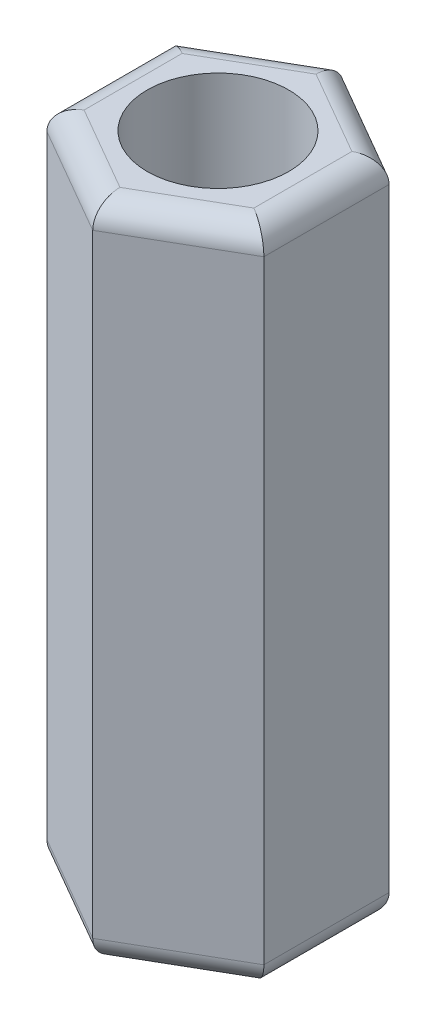
SolidWorks part; units mm, degrees
ref_plane "前视基准面" through (0, 0, 0) normal (0, 0, 1) x (1, 0, 0)
ref_plane "上视基准面" through (0, 0, 0) normal (0, 1, 0) x (1, 0, 0)
ref_plane "右视基准面" through (0, 0, 0) normal (1, 0, 0) x (0, 0, -1)
sketch "草图1" plane through (0, 0, 0) normal (0, 1, 0) x (1, 0, 0)
  line L1 (2.3, -1.3279) -> (2.3, 1.3279)
  line L2 (2.3, 1.3279) -> (0, 2.6558)
  line L3 (0, 2.6558) -> (-2.3, 1.3279)
  line L4 (-2.3, 1.3279) -> (-2.3, -1.3279)
  line L5 (-2.3, -1.3279) -> (0, -2.6558)
  line L6 (0, -2.6558) -> (2.3, -1.3279)
  circle A0 centre (0, 0) radius 2.3 construction
  circle A1 centre (0, 0) radius 1.5
  dimension "D2" = 3
  dimension "D1" = 4.6
extrude "凸台-拉伸1" add sketch "草图1" along normal blind 14
fillet "圆角1" radius 0.5 12 edges at (-1.15, 14, 1.9919) (-2.3, 14, 0) (-1.15, 14, -1.9919) (1.15, 14, -1.9919) (2.3, 14, 0) (1.15, 14, 1.9919) (-1.15, 0, 1.9919) (1.15, 0, 1.9919) (2.3, 0, 0) (1.15, 0, -1.9919) (-1.15, 0, -1.9919) (-2.3, 0, 0)
